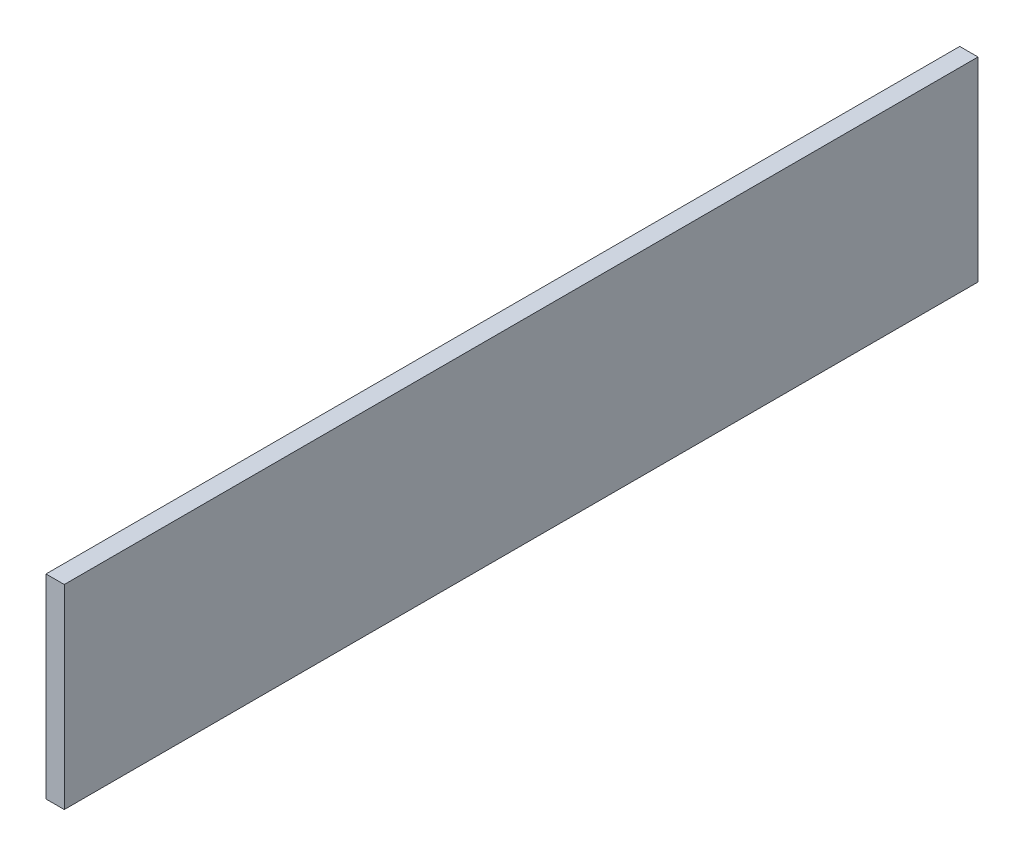
SolidWorks part; units mm, degrees
material "Ceramic Porcelain"
ref_plane "Front Plane" through (0, 0, 0) normal (0, 0, 1) x (1, 0, 0)
ref_plane "Top Plane" through (0, 0, 0) normal (0, 1, 0) x (1, 0, 0)
ref_plane "Right Plane" through (0, 0, 0) normal (1, 0, 0) x (0, 0, -1)
sketch "Sketch1" plane through (0, 0, 0) normal (1, 0, 0) x (0, 0, -1)
  line L1 (-851.8519, 418.0556) -> (648.1481, 418.0556)
  line L2 (-851.8519, 418.0556) -> (-851.8519, 98.0556)
  line L3 (-851.8519, 98.0556) -> (648.1481, 98.0556)
  line L4 (648.1481, 418.0556) -> (648.1481, 98.0556)
  dimension "D1" = 1500
  dimension "D2" = 320
extrude "Boss-Extrude1" add sketch "Sketch1" along normal blind 30
